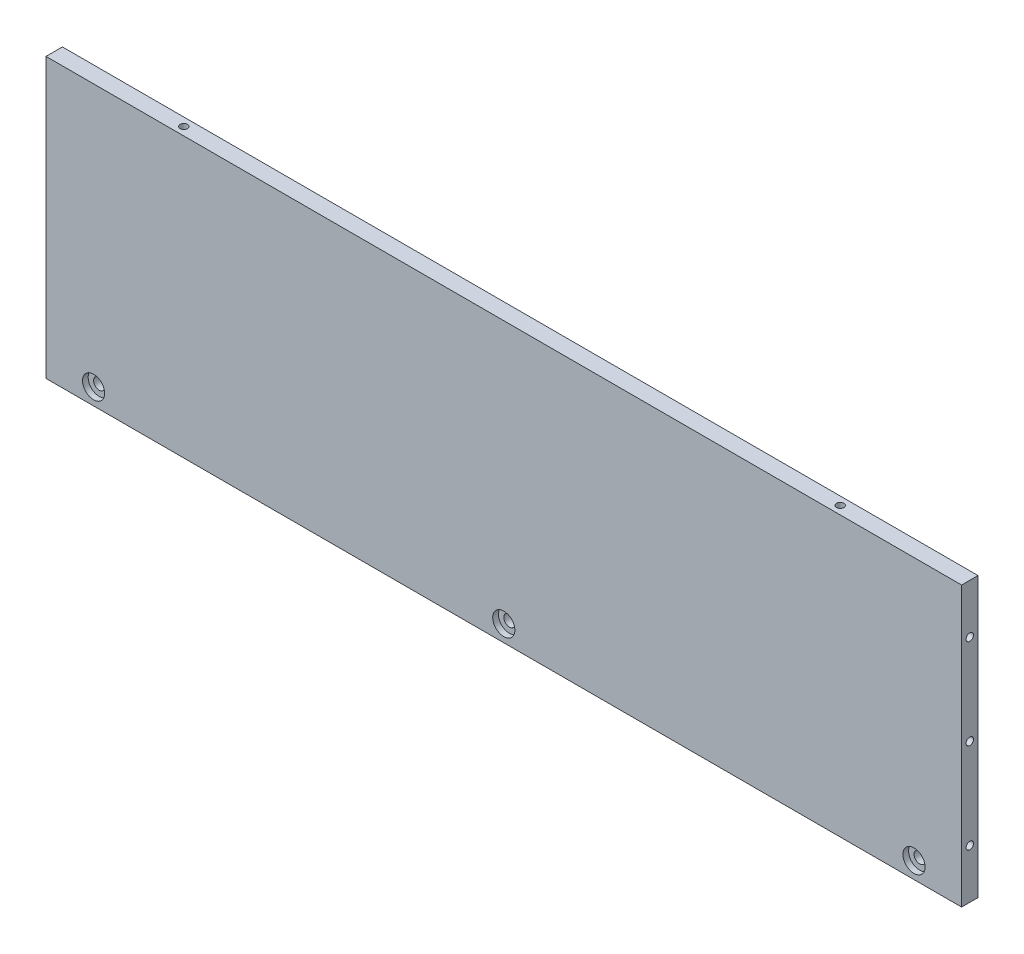
SolidWorks part; units mm, degrees
ref_plane "Front Plane" through (0, 0, 0) normal (0, 0, 1) x (1, 0, 0)
ref_plane "Top Plane" through (0, 0, 0) normal (0, 1, 0) x (1, 0, 0)
ref_plane "Right Plane" through (0, 0, 0) normal (1, 0, 0) x (0, 0, -1)
sketch "Sketch1" plane through (0, 0, 0) normal (0, 0, 1) x (1, 0, 0)
  line L1 (-130.9962, 78.0328) -> (148.0038, 78.0328)
  line L2 (-130.9962, 78.0328) -> (-130.9962, -6.9672)
  line L3 (-130.9962, -6.9672) -> (148.0038, -6.9672)
  line L4 (148.0038, 78.0328) -> (148.0038, -6.9672)
  dimension "D1" = 279
  dimension "D2" = 85
extrude "Boss-Extrude1" add sketch "Sketch1" along normal blind 5
sketch "Sketch2" plane through (0, 0, 5) normal (0, 0, 1) x (1, 0, 0)
  line L0 (-116.4962, -1.9672) -> (133.5038, -1.9672)
  line L1 (-130.9962, -6.9672) -> (148.0038, -6.9672) construction
  point P3 (8.5038, -1.9672)
  point P5 (8.5038, -6.9672)
  dimension "D1" = 5
  dimension "D2" = 250
  dimension "D3" = 0
hole_wizard "CBORE for #4 Binding Head Machine Screw1" positions "Sketch5" profile "Sketch4" counterbore size "#4" standard "ANSI Inch" end condition through all
sketch "Sketch5" plane through (0, 0, 5) normal (0, 0, 1) x (1, 0, 0)
  point P0 (-116.4962, -1.9672)
  point P3 (8.5038, -1.9672)
  point P6 (133.5038, -1.9672)
sketch "Sketch4" plane through (-116.4962, -1.9672, 5) normal (1, 0, 0) x (0, -1, 0)
  line L0 (0, 0) -> (0, 5)
  line L1 (0, 5) -> (1.7272, 5)
  line L3 (1.7272, 5) -> (1.7272, 1.7272)
  line L4 (1.7272, 1.7272) -> (3.3731, 1.7272)
  line L5 (3.3731, 1.7272) -> (3.3731, 0)
  line L7 (3.3731, 0) -> (0, 0)
  line L11 (0, -6.35) -> (0, 107.95) construction
  dimension "Thru Hole Dia." = 3.4544
  dimension "Thru Hole Depth" = 5
  dimension "C'Bore Dia." = 6.7462
  dimension "C'Bore Depth" = 1.7272
sketch "Sketch6" plane through (-130.9962, 0, 0) normal (-1, 0, 0) x (0, 0, 1)
  line L0 (0, 35.5328) -> (5, 35.5328)
  line L1 (0, 78.0328) -> (0, -6.9672) construction
  line L2 (5, 78.0328) -> (5, -6.9672) construction
  line L3 (2.5, 8.0328) -> (2.5, 63.0328)
  line L4 (5, 78.0328) -> (0, 78.0328) construction
  point P9 (2.5, 35.5328)
  dimension "D1" = 15
hole_wizard "#4-40 Tapped Hole1" positions "Sketch7" profile "Sketch8" tap size "#4-40" standard "ANSI Inch"
sketch "Sketch7" plane through (-130.9962, 0, 0) normal (-1, 0, 0) x (0, 0, 1)
  point P0 (2.5, 63.0328)
  point P3 (2.5, 35.5328)
  point P6 (2.5, 8.0328)
sketch "Sketch8" plane through (-130.9962, 63.0328, 2.5) normal (0, 1, 0) x (0, 0, 1)
  line L0 (0, 0) -> (0, 8.2792)
  line L1 (0, 8.2792) -> (1.1303, 7.6)
  line L2 (1.1303, 7.6) -> (1.1303, 0)
  line L5 (1.1303, 0) -> (0, 0)
  line L10 (0, 8.2792) -> (-1.1303, 7.6) construction
  line L11 (0, -6.35) -> (0, 107.95) construction
  dimension "Tap Drill Dia." = 2.2606
  dimension "Tap Drill Depth" = 7.6
  dimension "Drill Angle" = 118
cosmetic thread "Hole Thread1" parameters "D1"=5.69, "D2"=2.8448
cosmetic thread "Hole Thread2" parameters "D1"=5.69, "D2"=2.8448
cosmetic thread "Hole Thread3" parameters "D1"=5.69, "D2"=2.8448
sketch "Sketch9" plane through (148.0038, 0, 0) normal (1, 0, 0) x (0, 0, -1)
  line L0 (-2.5, 8.0328) -> (-2.5, 63.0328)
  point P3 (-2.5, 35.5328)
hole_wizard "#4-40 Tapped Hole2" positions "Sketch10" profile "Sketch11" tap size "#4-40" standard "ANSI Inch"
sketch "Sketch10" plane through (148.0038, 0, 0) normal (1, 0, 0) x (0, 0, -1)
  line L0 (0, 35.5328) -> (-5, 35.5328) construction
  point P0 (-2.5, 63.0328)
  point P3 (-2.5, 35.5328)
  point P7 (-2.5, 8.0328)
sketch "Sketch11" plane through (148.0038, 63.0328, 2.5) normal (0, 1, 0) x (0, 0, -1)
  line L0 (0, 0) -> (0, 8.2792)
  line L1 (0, 8.2792) -> (1.1303, 7.6)
  line L2 (1.1303, 7.6) -> (1.1303, 0)
  line L5 (1.1303, 0) -> (0, 0)
  line L10 (0, 8.2792) -> (-1.1303, 7.6) construction
  line L11 (0, -6.35) -> (0, 107.95) construction
  dimension "Tap Drill Dia." = 2.2606
  dimension "Tap Drill Depth" = 7.6
  dimension "Drill Angle" = 118
cosmetic thread "Hole Thread4" parameters "D1"=5.69, "D2"=2.8448
cosmetic thread "Hole Thread5" parameters "D1"=5.69, "D2"=2.8448
cosmetic thread "Hole Thread6" parameters "D1"=5.69, "D2"=2.8448
sketch "Sketch12" plane through (0, 78.0328, 0) normal (0, 1, 0) x (1, 0, 0)
  line L0 (-130.9962, -2.5) -> (148.0038, -2.5)
  line L1 (-130.9962, 0) -> (-130.9962, -5) construction
  line L2 (8.5038, -5) -> (8.5038, 0)
  line L3 (148.0038, 0) -> (-130.9962, 0) construction
  point P10 (-91.4962, -2.5)
  point P11 (108.5038, -2.5)
  dimension "D1" = 100
hole_wizard "#4-40 Tapped Hole3" positions "Sketch13" profile "Sketch14" tap size "#4-40" standard "ANSI Inch"
sketch "Sketch13" plane through (0, 78.0328, 0) normal (0, 1, 0) x (1, 0, 0)
  point P0 (-91.4962, -2.5)
  point P3 (108.5038, -2.5)
sketch "Sketch14" plane through (-91.4962, 78.0328, 2.5) normal (1, 0, 0) x (0, 0, 1)
  line L0 (0, 0) -> (0, 8.2792)
  line L1 (0, 8.2792) -> (1.1303, 7.6)
  line L2 (1.1303, 7.6) -> (1.1303, 0)
  line L5 (1.1303, 0) -> (0, 0)
  line L10 (0, 8.2792) -> (-1.1303, 7.6) construction
  line L11 (0, -6.35) -> (0, 107.95) construction
  dimension "Tap Drill Dia." = 2.2606
  dimension "Tap Drill Depth" = 7.6
  dimension "Drill Angle" = 118
cosmetic thread "Hole Thread7" parameters "D1"=5.69, "D2"=2.8448
cosmetic thread "Hole Thread8" parameters "D1"=5.69, "D2"=2.8448
